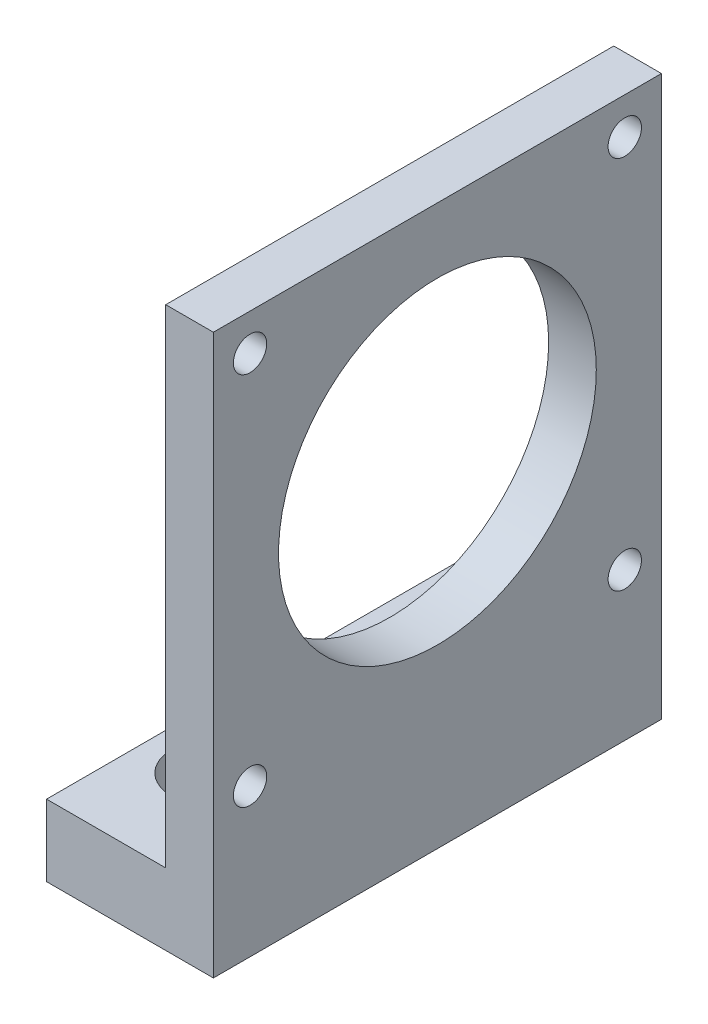
SolidWorks part; units mm, degrees
ref_plane "前视基准面" through (0, 0, 0) normal (0, 0, 1) x (1, 0, 0)
ref_plane "上视基准面" through (0, 0, 0) normal (0, 1, 0) x (1, 0, 0)
ref_plane "右视基准面" through (0, 0, 0) normal (1, 0, 0) x (0, 0, -1)
sketch "草图1" plane through (0, 0, 0) normal (0, 0, 1) x (1, 0, 0)
  line L1 (0, 0) -> (6, 0)
  line L2 (0, 0) -> (0, 62.4)
  line L3 (0, 62.4) -> (6, 62.4)
  line L4 (6, 0) -> (6, 62.4)
  dimension "D1" = 62.4
  dimension "D2" = 6
extrude "凸台-拉伸1" add sketch "草图1" along normal blind 56.4
sketch "草图3" plane through (0, 0, 0) normal (-1, 0, 0) x (0, 0, 1)
  line L0 (56.4, 62.4) -> (56.4, 0) construction
  line L1 (0, 0) -> (56.4, 0)
  line L2 (0, 0) -> (0, 6)
  line L3 (0, 6) -> (56.4, 6)
  line L4 (56.4, 0) -> (56.4, 6)
  dimension "D1" = 6
extrude "凸台-拉伸3" add sketch "草图3" along normal blind 15
hole_wizard "M5 螺纹孔1" positions "草图4" profile "草图5" tap size "M5" standard "ISO"
sketch "草图4" plane through (6, 0, 0) normal (1, 0, 0) x (0, 0, -1)
  line L2 (-56.4, 0) -> (0, 0) construction
  line L4 (-56.4, 6) -> (0, 6) construction
  line L5 (-56.4, 0) -> (-56.4, 62.4) construction
  line L6 (0, 0) -> (0, 62.4) construction
  line L8 (-28.2, 6) -> (-28.2, 62.4) construction
  line L9 (-56.4, 62.4) -> (0, 62.4) construction
  line L10 (-28.2, 62.4) -> (-28.2, 34.2) construction
  line L11 (-28.2, 34.2) -> (-5.0462, 34.2) construction
  point P0 (-51.785, 57.785)
  point P26 (-4.615, 57.785)
  point P27 (-4.615, 10.615)
  point P28 (-51.785, 10.615)
  dimension "D1" = 6
  dimension "D2" = 47.17
  dimension "D3" = 47.17
sketch "草图5" plane through (6, 57.785, 51.785) normal (0, 1, 0) x (0, 0, -1)
  line L0 (0, 0) -> (0, 13.6618)
  line L1 (0, 13.6618) -> (2.1, 12.4)
  line L2 (2.1, 12.4) -> (2.1, 0)
  line L5 (2.1, 0) -> (0, 0)
  line L10 (0, 13.6618) -> (-2.1, 12.4) construction
  line L11 (0, -6.35) -> (0, 107.95) construction
  dimension "螺纹孔钻头直径" = 4.2
  dimension "螺纹孔钻头深度" = 12.4
  dimension "导头角度" = 118
cosmetic thread "孔螺蚊线1" parameters "D1"=6, "D2"=5
cosmetic thread "孔螺蚊线2" parameters "D1"=6, "D2"=5
cosmetic thread "孔螺蚊线3" parameters "D1"=6, "D2"=5
cosmetic thread "孔螺蚊线4" parameters "D1"=6, "D2"=5
sketch "草图6" plane through (6, 0, 0) normal (1, 0, 0) x (0, 0, -1)
  line L0 (-51.785, 57.785) -> (-51.785, 10.615) construction
  line L1 (-51.785, 10.615) -> (-4.615, 10.615) construction
  line L2 (-4.615, 10.615) -> (-28.2, 10.615) construction
  line L3 (-28.2, 10.615) -> (-28.2, 34.2) construction
  circle A0 centre (-28.2, 34.2) radius 20
  dimension "D1" = 40
extrude "切除-拉伸1" cut sketch "草图6" against normal blind 15
sketch "草图7" plane through (0, 0, 0) normal (0, -1, 0) x (1, 0, 0)
  line L1 (6, 0) -> (-15, 0)
  line L2 (6, 0) -> (6, 56.4)
  line L3 (6, 56.4) -> (-15, 56.4)
  line L4 (-15, 0) -> (-15, 56.4)
extrude "凸台-拉伸4" add sketch "草图7" along normal blind 8
sketch "草图8" plane through (0, 6, 0) normal (0, 1, 0) x (1, 0, 0)
  line L1 (-15, 0) -> (0, 0)
  line L2 (-15, 0) -> (-15, -56.4)
  line L3 (-15, -56.4) -> (0, -56.4)
  line L4 (0, 0) -> (0, -56.4)
extrude "切除-拉伸2" cut sketch "草图8" against normal blind 5
hole_wizard "M5 六角凹头螺钉的柱形沉头孔1" positions "草图9" profile "草图10" counterbore size "M5" standard "ISO"
sketch "草图9" plane through (0, 1, 0) normal (0, 1, 0) x (1, 0, 0)
  line L0 (0, -28.2) -> (-15, -28.2) construction
  line L1 (0, -56.4) -> (0, 0) construction
  line L2 (-15, 0) -> (-15, -56.4) construction
  line L3 (-15, -28.2) -> (-7.5, -28.2) construction
  line L4 (-7.5, -28.2) -> (-7.5, -59.3821) construction
  point P0 (-7.5, -13.2)
  point P2 (-7.5, -43.2)
  point P16 (0, 0)
  point P17 (0, 0)
  point P18 (0, 0)
  point P19 (0, 0)
  dimension "D1" = 30
sketch "草图10" plane through (-7.5, 1, 13.2) normal (1, 0, 0) x (0, 0, 1)
  line L0 (0, 0) -> (0, 14.0524)
  line L1 (0, 14.0524) -> (2.75, 12.4)
  line L2 (2.75, 12.4) -> (2.75, 5.4)
  line L3 (2.75, 5.4) -> (5, 5.4)
  line L4 (5, 5.4) -> (5, 0)
  line L5 (5, 0) -> (0, 0)
  line L10 (0, 14.0524) -> (-2.75, 12.4) construction
  line L11 (0, -6.35) -> (0, 107.95) construction
  dimension "孔直径" = 5.5
  dimension "孔深度" = 12.4
  dimension "柱形沉头孔直径" = 10
  dimension "柱形沉头孔深度" = 5.4
  dimension "导头角度" = 118
sketch "草图11" plane through (0, 1, 0) normal (0, 1, 0) x (1, 0, 0)
  line L1 (-2.5, -13.2) -> (-12.5, -13.2)
  line L2 (-2.5, -13.2) -> (-2.5, -43.2)
  line L3 (-2.5, -43.2) -> (-12.5, -43.2)
  line L4 (-12.5, -13.2) -> (-12.5, -43.2)
  circle A0 centre (-7.5, -13.2) radius 5 construction
  circle A1 centre (-7.5, -43.2) radius 5 construction
extrude "切除-拉伸3" cut sketch "草图11" against normal up to surface (5.4 mm away) up to face at (-7.5, -4.4, 15.95)
sketch "草图12" plane through (0, -4.4, 0) normal (0, 1, 0) x (1, 0, 0)
  line L1 (-4.75, -13.2) -> (-10.25, -13.2)
  line L2 (-4.75, -13.2) -> (-4.75, -43.2)
  line L3 (-4.75, -43.2) -> (-10.25, -43.2)
  line L4 (-10.25, -13.2) -> (-10.25, -43.2)
  circle A0 centre (-7.5, -13.2) radius 2.75 construction
  circle A1 centre (-7.5, -43.2) radius 2.75 construction
extrude "切除-拉伸4" cut sketch "草图12" against normal blind 10
